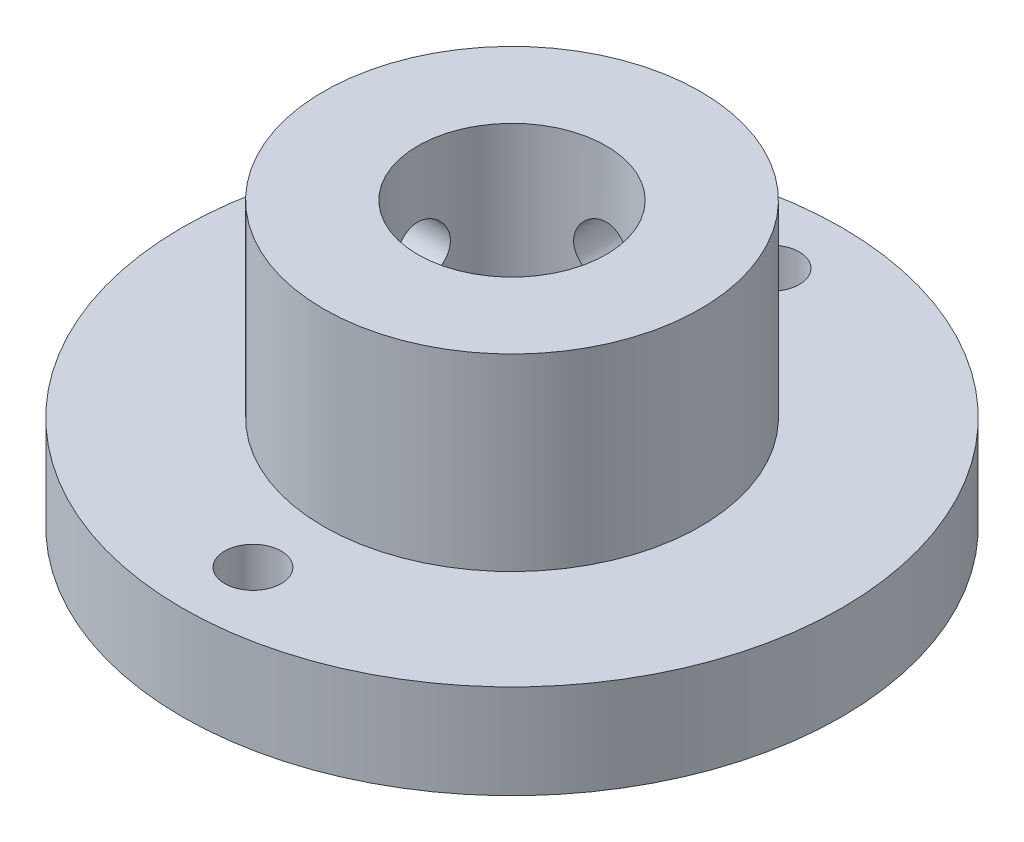
SolidWorks part; units mm, degrees
material "Náilon 101"
ref_plane "Plano frontal" through (0, 0, 0) normal (0, 0, 1) x (1, 0, 0)
ref_plane "Plano superior" through (0, 0, 0) normal (0, 1, 0) x (1, 0, 0)
ref_plane "Plano direito" through (0, 0, 0) normal (1, 0, 0) x (0, 0, -1)
sketch "Esboço1" plane through (0, 0, 0) normal (0, 1, 0) x (1, 0, 0)
  circle A0 centre (0, 0) radius 17.5
  dimension "D1" = 35
extrude "Ressalto-extrusão1" add sketch "Esboço1" along normal blind 5
sketch "Esboço2" plane through (0, 5, 0) normal (0, 1, 0) x (1, 0, 0)
  circle A0 centre (0, 0) radius 10
  dimension "D1" = 20
extrude "Ressalto-extrusão2" add sketch "Esboço2" along normal blind 10
sketch "Esboço3" plane through (0, 15, 0) normal (0, 1, 0) x (1, 0, 0)
  circle A0 centre (0, 0) radius 5
  dimension "D1" = 10
extrude "Corte-extrusão1" cut sketch "Esboço3" against normal through all
sketch "Esboço4" plane through (0, 5, 0) normal (0, 1, 0) x (1, 0, 0)
  line L0 (0, 10) -> (0, 17.5) construction
  circle A0 centre (0, 0) radius 10 construction
  circle A1 centre (0, 0) radius 10 construction
  circle A2 centre (0, 0) radius 17.5 construction
  circle A3 centre (0, 13.75) radius 1.5
  circle A7 centre (0, -13.75) radius 1.5
  point P15 (0, 0)
  point P20 (0, 0)
  dimension "D1" = 3
  dimension "D2" = 2
extrude "Corte-extrusão2" cut sketch "Esboço4" against normal blind 10
sketch "Esboço5" plane through (0, 0, 0) normal (0, 0, 1) x (1, 0, 0)
  line L0 (0, 5) -> (0, 15) construction
  line L1 (17.5, 5) -> (-17.5, 5) construction
  line L2 (10, 15) -> (-10, 15) construction
  circle A0 centre (0, 10) radius 1.5
  dimension "D1" = 3
extrude "Corte-extrusão3" cut sketch "Esboço5" against normal through all
sketch "Esboço6" plane through (0, 0, 0) normal (1, 0, 0) x (0, 0, -1)
  line L0 (0, 5) -> (0, 15) construction
  line L1 (17.5, 5) -> (-17.5, 5) construction
  line L2 (5, 15) -> (-5, 15) construction
  circle A0 centre (0, 10) radius 1.5
  dimension "D1" = 3
extrude "Corte-extrusão4" cut sketch "Esboço6" against normal blind 10
